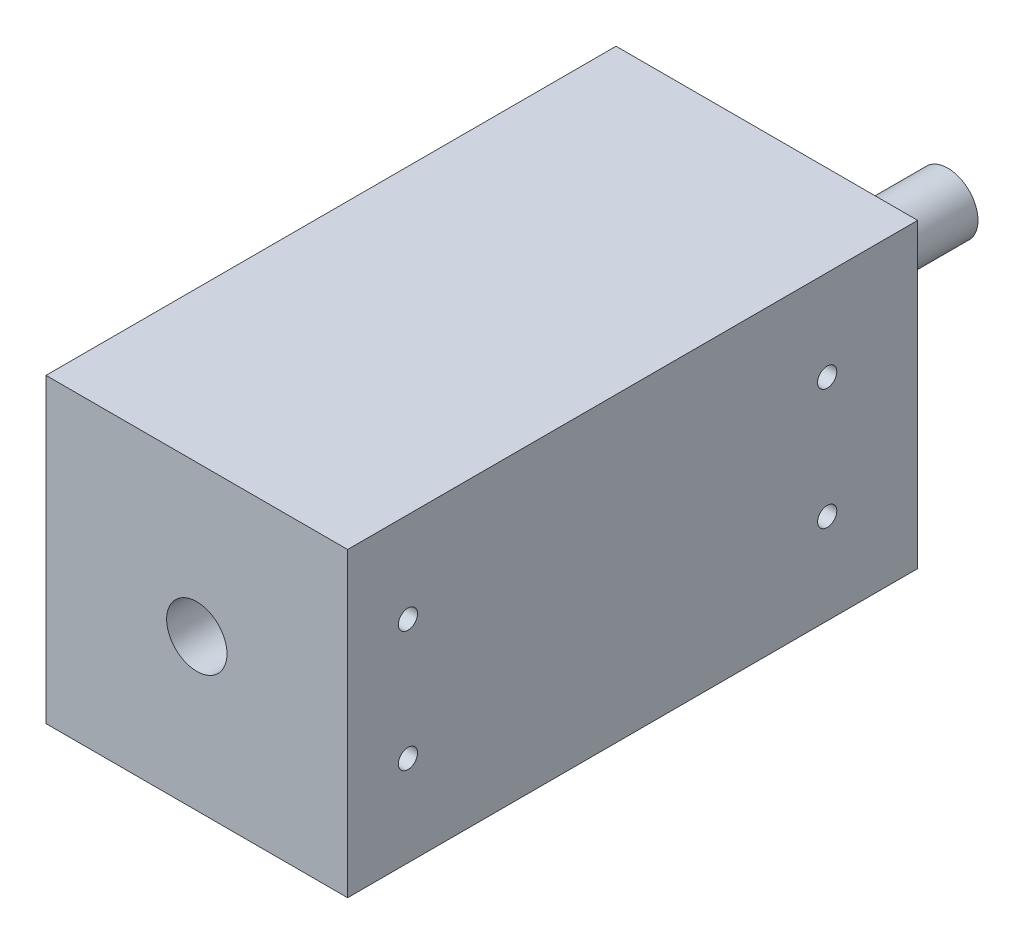
SolidWorks part; units mm, degrees
ref_plane "Front Plane" through (0, 0, 0) normal (0, 0, 1) x (1, 0, 0)
ref_plane "Top Plane" through (0, 0, 0) normal (0, 1, 0) x (1, 0, 0)
ref_plane "Right Plane" through (0, 0, 0) normal (1, 0, 0) x (0, 0, -1)
sketch "Sketch1" plane through (0, 0, 0) normal (0, 0, 1) x (1, 0, 0)
  line L1 (-31.75, 31.75) -> (31.75, 31.75)
  line L2 (-31.75, 31.75) -> (-31.75, -31.75)
  line L3 (-31.75, -31.75) -> (31.75, -31.75)
  line L4 (31.75, 31.75) -> (31.75, -31.75)
  line L5 (-31.75, 31.75) -> (31.75, -31.75) construction
  line L6 (-31.75, -31.75) -> (31.75, 31.75) construction
  point P0 (0, 0)
  dimension "D1" = 63.5
extrude "Boss-Extrude1" add sketch "Sketch1" along normal mid plane 120.015
sketch "Sketch2" plane through (0, 0, -60.0075) normal (0, 0, -1) x (-1, 0, 0)
  circle A0 centre (0, 0) radius 6.35
  dimension "D1" = 12.7
extrude "Boss-Extrude2" add sketch "Sketch2" along normal blind 38.1
sketch "Sketch3" plane through (0, 0, 60.0075) normal (0, 0, 1) x (1, 0, 0)
  circle A0 centre (0, 0) radius 6.35
  dimension "D1" = 12.7
extrude "Cut-Extrude1" cut sketch "Sketch3" against normal blind 38.1
sketch "Sketch4" plane through (-31.75, 0, 0) normal (-1, 0, 0) x (0, 0, 1)
  line L0 (0, 12.7) -> (0, -12.7) construction
  line L1 (-40.9575, -12.7) -> (47.3075, -12.7) construction
  line L2 (-40.9575, -12.7) -> (-40.9575, 12.7) construction
  line L3 (-40.9575, 12.7) -> (47.3075, 12.7) construction
  line L4 (47.3075, -12.7) -> (47.3075, 12.7) construction
  line L5 (-60.0075, 31.75) -> (-60.0075, -31.75) construction
  line L6 (60.0075, 31.75) -> (60.0075, -31.75) construction
  point P4 (0, 0)
  point P8 (0, 0)
  dimension "D1" = 25.4
  dimension "D2" = 19.05
  dimension "D3" = 12.7
hole_wizard "#10-32 Tapped Hole1" positions "Sketch5" profile "Sketch6" tap size "#10-32" standard "ANSI Inch" end condition through all
sketch "Sketch5" plane through (-31.75, 0, 0) normal (-1, 0, 0) x (0, 0, 1)
  point P0 (-40.9575, 12.7)
  point P3 (-40.9575, -12.7)
  point P6 (47.3075, -12.7)
  point P9 (47.3075, 12.7)
sketch "Sketch6" plane through (-31.75, 12.7, -40.9575) normal (0, 1, 0) x (0, 0, 1)
  line L0 (0, 0) -> (0, 63.5)
  line L1 (0, 63.5) -> (2.0193, 63.5)
  line L2 (2.0193, 63.5) -> (2.0193, 0)
  line L5 (2.0193, 0) -> (0, 0)
  line L11 (0, -6.35) -> (0, 107.95) construction
  dimension "Thru Tap Drill Dia." = 4.0386
  dimension "Thru Tap Drill Depth" = 63.5
cosmetic thread "Hole Thread1" parameters "D2"=4.826
cosmetic thread "Hole Thread2" parameters "D2"=4.826
cosmetic thread "Hole Thread3" parameters "D2"=4.826
cosmetic thread "Hole Thread4" parameters "D2"=4.826
